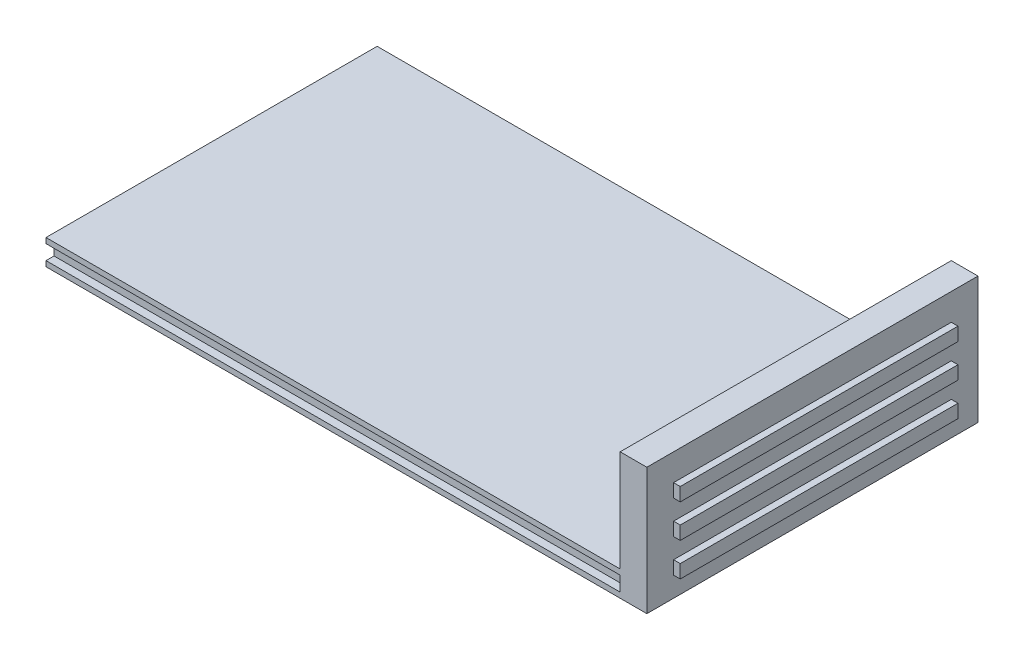
SolidWorks part; units mm, degrees
ref_plane "Front Plane" through (0, 0, 0) normal (0, 0, 1) x (1, 0, 0)
ref_plane "Top Plane" through (0, 0, 0) normal (0, 1, 0) x (1, 0, 0)
ref_plane "Right Plane" through (0, 0, 0) normal (1, 0, 0) x (0, 0, -1)
sketch "Sketch1" plane through (0, 0, 0) normal (0, 1, 0) x (1, 0, 0)
  line L1 (-45, -24.8) -> (45, -24.8)
  line L2 (-45, -24.8) -> (-45, 24.8)
  line L3 (-45, 24.8) -> (45, 24.8)
  line L4 (45, -24.8) -> (45, 24.8)
  line L5 (-45, -24.8) -> (45, 24.8) construction
  line L6 (-45, 24.8) -> (45, -24.8) construction
  point P0 (0, 0)
  dimension "D1" = 49.6
  dimension "D2" = 90
extrude "Boss-Extrude1" add sketch "Sketch1" along normal blind 3.8
sketch "Sketch2" plane through (45, 0, 0) normal (1, 0, 0) x (0, 0, -1)
  line L0 (-24.8, 3.8) -> (-24.8, 0) construction
  line L1 (-24.8, 3) -> (-23.6, 3)
  line L2 (-24.8, 3) -> (-24.8, 0.8)
  line L3 (-24.8, 0.8) -> (-23.6, 0.8)
  line L4 (-23.6, 3) -> (-23.6, 0.8)
  point P6 (-23.6, 1.9)
  point P7 (-24.8, 1.9)
  dimension "D1" = 1.2
  dimension "D2" = 2.2
extrude "Cut-Extrude1" cut sketch "Sketch2" against normal through all
mirror "Mirror1" about plane through (0, 0, 0) normal (0, 0, 1) of "Cut-Extrude1"
sketch "Sketch3" plane through (0, 0, 0) normal (0, -1, 0) x (1, 0, 0)
  line L0 (45, -24.8) -> (-45, -24.8) construction
  line L1 (45, 24.8) -> (41, 24.8)
  line L2 (45, 24.8) -> (45, -24.8)
  line L3 (45, -24.8) -> (41, -24.8)
  line L4 (41, 24.8) -> (41, -24.8)
  dimension "D1" = 4
extrude "Boss-Extrude2" add sketch "Sketch3" against normal blind 19
sketch "Sketch4" plane through (45, 0, 0) normal (1, 0, 0) x (0, 0, -1)
  line L0 (-24.8, 19) -> (-24.8, 0) construction
  line L1 (-20.8, 15) -> (20.8, 15)
  line L2 (-20.8, 15) -> (-20.8, 13)
  line L3 (-20.8, 13) -> (20.8, 13)
  line L4 (20.8, 15) -> (20.8, 13)
  line L5 (24.8, 19) -> (-24.8, 19) construction
  line L6 (24.8, 19) -> (24.8, 0) construction
  dimension "D1" = 2
  dimension "D2" = 4
  dimension "D3" = 4
  dimension "4" = 4
extrude "Boss-Extrude3" add sketch "Sketch4" along normal blind 1
pattern_linear "LPattern1" count 3 spacing 5 along (0, -1, 0) of "Boss-Extrude3"
